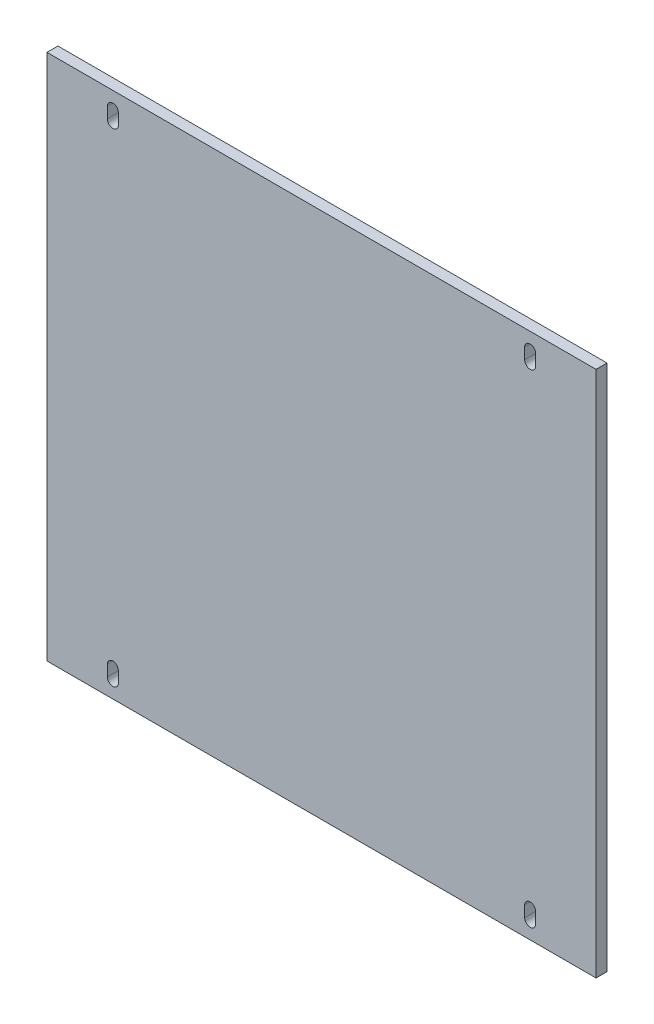
SolidWorks part; units mm, degrees
material "Pin"
ref_plane "Front" through (0, 0, 0) normal (0, 0, 1) x (1, 0, 0)
ref_plane "Top" through (0, 0, 0) normal (0, 1, 0) x (1, 0, 0)
ref_plane "Right" through (0, 0, 0) normal (1, 0, 0) x (0, 0, -1)
sketch "Esquisse1" plane through (0, 0, 0) normal (0, 0, 1) x (1, 0, 0)
  line L1 (0, 0) -> (250, 0)
  line L2 (0, 0) -> (0, 240)
  line L3 (0, 240) -> (250, 240)
  line L4 (250, 0) -> (250, 240)
  dimension "D1" = 240
  dimension "D2" = 250
extrude "Boss.-Extru.1" add sketch "Esquisse1" along normal blind 5
sketch "Esquisse2" plane through (0, 0, 0) normal (0, 0, 1) x (1, 0, 0)
  line L0 (30, 7.5) -> (30, 12.5) construction
  line L1 (27.5, 7.5) -> (27.5, 12.5)
  line L2 (32.5, 7.5) -> (32.5, 12.5)
  line L4 (0, 240) -> (0, 0) construction
  line L5 (0, 0) -> (250, 0) construction
  arc A0 (27.5, 7.5) -> (32.5, 7.5) centre (30, 7.5) ccw
  arc A1 (32.5, 12.5) -> (27.5, 12.5) centre (30, 12.5) ccw
  point P2 (30, 10)
  dimension "D1" = 2.5
  dimension "D2" = 5
  dimension "D3" = 30
  dimension "D4" = 10
extrude "Enlèv. mat.-Extru.1" cut sketch "Esquisse2" along normal blind 5
pattern_linear "Répétition linéaire1" count 2 spacing 220 along (0, 1, 0) count 2 spacing 190 along (1, 0, 0) of "Enlèv. mat.-Extru.1"
